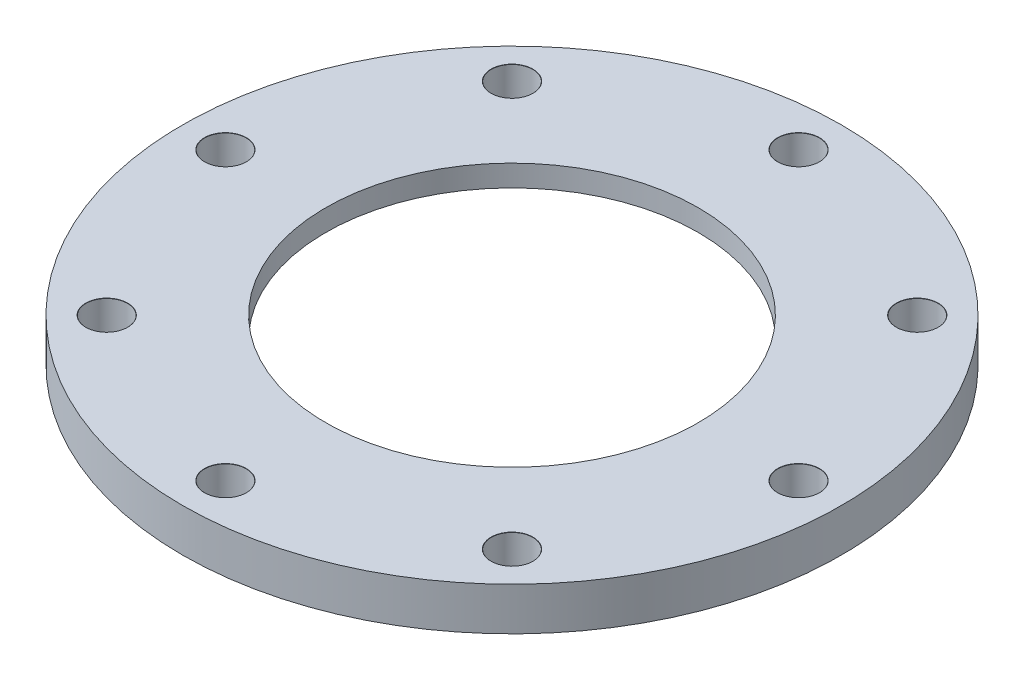
SolidWorks part; units mm, degrees
material "1.4305 (X8CrNiS18-9)"
ref_plane "Ebene vorne" through (0, 0, 0) normal (0, 0, 1) x (1, 0, 0)
ref_plane "Ebene oben" through (0, 0, 0) normal (0, 1, 0) x (1, 0, 0)
ref_plane "Ebene rechts" through (0, 0, 0) normal (1, 0, 0) x (0, 0, -1)
sketch "Sketch1" plane through (0, 0, 0) normal (0, 0, 1) x (1, 0, 0)
  line L0 (0, 0) -> (0, 26.8831) construction
  line L1 (-32, 0) -> (-46, 0)
  line L2 (-46, 0) -> (-46, 6)
  line L3 (-46, 6) -> (-26, 6)
  line L4 (-26, 6) -> (-26, 3)
  line L5 (-26, 3) -> (-32, 3)
  line L6 (-32, 3) -> (-32, 0)
  dimension "D1" = 32
  dimension "D2" = 92
  dimension "D3" = 26
  dimension "D4" = 3
  dimension "D5" = 3
revolve "Revolve1" add sketch "Sketch1" angle 360 about L0
hole_wizard "M5 Clearance Hole1" positions "Sketch2" profile "Sketch3" hole size "M5" standard "DIN" end condition up to next
sketch "Sketch2" plane through (0, 6, 0) normal (0, 1, 0) x (1, 0, 0)
  point P0 (40, 0)
  dimension "D1" = 40
sketch "Sketch3" plane through (40, 6, 0) normal (1, 0, 0) x (0, 0, 1)
  line L0 (0, 0) -> (0, 6)
  line L1 (0, 6) -> (2.9, 6)
  line L2 (2.9, 6) -> (2.9, 0.025)
  line L3 (2.9, 0.025) -> (2.925, 0)
  line L5 (2.925, 0) -> (0, 0)
  line L6 (-2.9, 0.025) -> (-2.925, 0) construction
  line L11 (0, -6.35) -> (0, 107.95) construction
  dimension "Thru Hole Dia." = 5.8
  dimension "Thru Hole Depth" = 6
  dimension "Near C'Sink Dia." = 5.85
  dimension "Near C'Sink Angle" = 90
pattern_circular "CirPattern1" count 8 over 360 about axis through (0, 0, 0) along (0, 1, 0) of "M5 Clearance Hole1"
